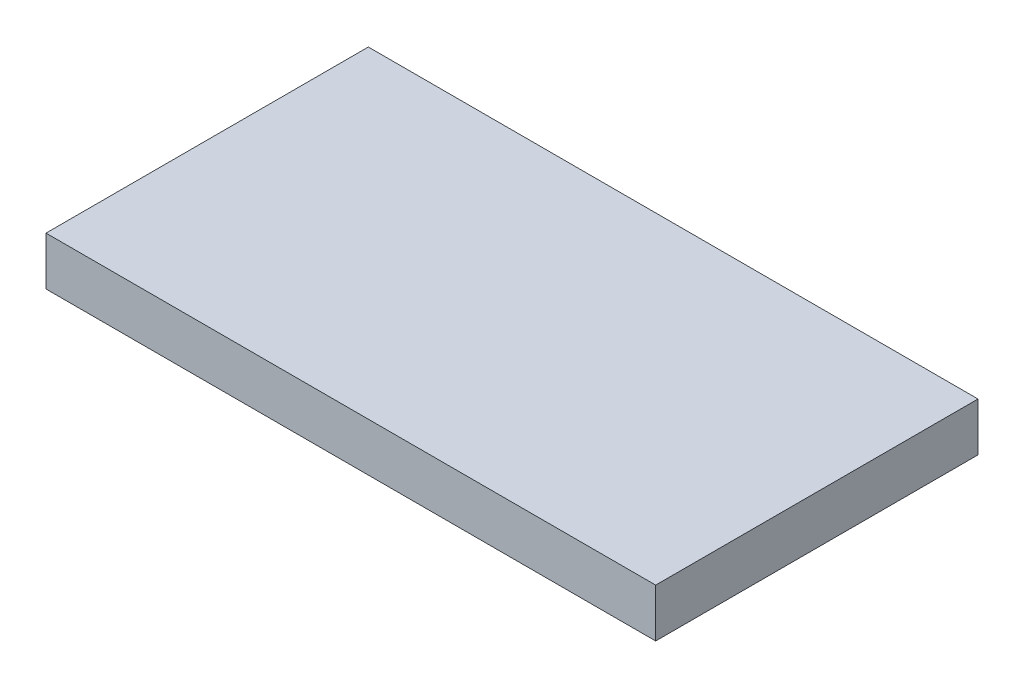
SolidWorks part; units mm, degrees
ref_plane "Front Plane" through (0, 0, 0) normal (0, 0, 1) x (1, 0, 0)
ref_plane "Top Plane" through (0, 0, 0) normal (0, 1, 0) x (1, 0, 0)
ref_plane "Right Plane" through (0, 0, 0) normal (1, 0, 0) x (0, 0, -1)
sketch "Sketch1" plane through (0, 0, 0) normal (0, 1, 0) x (1, 0, 0)
  line L1 (0, 0) -> (59.959, 0)
  line L2 (0, 0) -> (0, 31.7)
  line L3 (0, 31.7) -> (59.959, 31.7)
  line L4 (59.959, 0) -> (59.959, 31.7)
  dimension "D1" = 59.959
  dimension "D2" = 31.7
extrude "Boss-Extrude1" add sketch "Sketch1" along normal blind 4.7625
